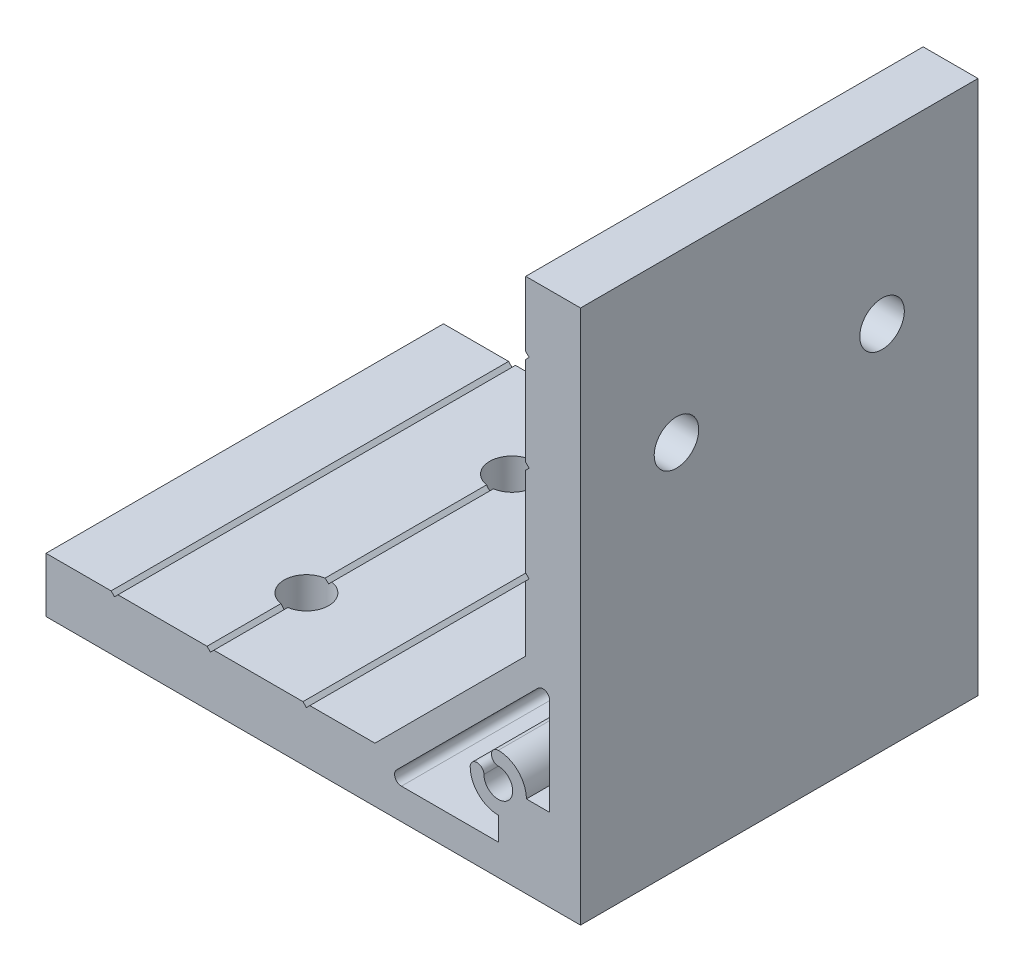
SolidWorks part; units mm, degrees
material "6063 T5"
ref_plane "Спереди" through (0, 0, 0) normal (0, 0, 1) x (1, 0, 0)
ref_plane "Сверху" through (0, 0, 0) normal (0, 1, 0) x (1, 0, 0)
ref_plane "Справа" through (0, 0, 0) normal (1, 0, 0) x (0, 0, -1)
sketch "Эскиз1" plane through (0, 0, 0) normal (0, 0, 1) x (1, 0, 0)
  line L0 (-78, 0) -> (0, 0)
  line L1 (0, 0) -> (0, 78)
  line L3 (-8, 53.5) -> (-8, 40.5)
  line L4 (-8, 40.5) -> (-7.5, 40)
  line L5 (-7.5, 40) -> (-8, 39.5)
  line L6 (-8, 39.5) -> (-8, 30)
  line L7 (-8, 30) -> (-30, 8)
  line L8 (-30, 8) -> (-39.5, 8)
  line L9 (-39.5, 8) -> (-40, 7.5)
  line L10 (-40, 7.5) -> (-40.5, 8)
  line L11 (-40.5, 8) -> (-53.5, 8)
  line L13 (-4.5, 12) -> (-4.5, 26.136)
  line L14 (-6.2071, 26.8431) -> (-26.8431, 6.2071)
  line L15 (-26.136, 4.5) -> (-12, 4.5)
  line L16 (-12, 4.5) -> (-12, 7.9)
  line L17 (-7.9, 12) -> (-4.5, 12)
  line L18 (-8, 53.5) -> (-7.5, 54)
  line L19 (-7.5, 54) -> (-8, 54.5)
  line L20 (-8, 54.5) -> (-8, 67.5)
  line L21 (-8, 67.5) -> (-7.5, 68)
  line L22 (-7.5, 68) -> (-8, 68.5)
  line L23 (-8, 68.5) -> (-8, 78)
  line L24 (-8, 78) -> (0, 78)
  line L25 (-53.5, 8) -> (-54, 7.5)
  line L26 (-54, 7.5) -> (-54.5, 8)
  line L27 (-54.5, 8) -> (-67.5, 8)
  line L28 (-67.5, 8) -> (-68, 7.5)
  line L29 (-68, 7.5) -> (-68.5, 8)
  line L30 (-68.5, 8) -> (-78, 8)
  line L31 (-78, 8) -> (-78, 0)
  arc A0 (-4.5, 26.136) -> (-6.2071, 26.8431) centre (-5.5, 26.136) ccw
  arc A1 (-26.8431, 6.2071) -> (-26.136, 4.5) centre (-26.136, 5.5) ccw
  arc A2 (-12, 7.9) -> (-16.1, 12) centre (-12, 12) cw
  arc A3 (-16.1, 12) -> (-14.1, 12) centre (-15.1, 12) cw
  arc A4 (-14.1, 12) -> (-12, 14.1) centre (-12, 12) ccw
  arc A5 (-12, 14.1) -> (-12, 16.1) centre (-12, 15.1) cw
  arc A6 (-12, 16.1) -> (-7.9, 12) centre (-12, 12) cw
  dimension "D6" = 4.2
  dimension "D7" = 1
  dimension "D9" = 1
  dimension "D2" = 8
  dimension "D3" = 135
  dimension "D4" = 12
  dimension "D5" = 12
  dimension "D8" = 30
  dimension "D10" = 3.5
  dimension "D11" = 4.5
  dimension "D12" = 40
  dimension "D13" = 1
  dimension "D14" = 54
  dimension "D15" = 68
  dimension "D16" = 78
extrude "Бобышка-Вытянуть1" add sketch "Эскиз1" along normal mid plane 58
sketch "Эскиз2" plane through (-8, 0, 0) normal (-1, 0, 0) x (0, 0, 1)
  line L1 (29, 54) -> (-29, 54) construction
  line L2 (-15, 54) -> (15, 54) construction
  circle A0 centre (-15, 54) radius 3.25
  circle A1 centre (15, 54) radius 3.25
  point P2 (0, 54)
  dimension "D1" = 6.5
  dimension "D2" = 30
extrude "Вырез-Вытянуть1" cut sketch "Эскиз2" against normal through all
sketch "Эскиз3" plane through (0, 8, 0) normal (0, 1, 0) x (1, 0, 0)
  line L1 (-54, -29) -> (-54, 29) construction
  line L2 (-54, 15) -> (-54, -15) construction
  circle A0 centre (-54, -15) radius 3.25
  circle A1 centre (-54, 15) radius 3.25
  point P2 (-54, 0)
  dimension "D1" = 6.5
  dimension "D2" = 30
extrude "Вырез-Вытянуть2" cut sketch "Эскиз3" against normal through all
